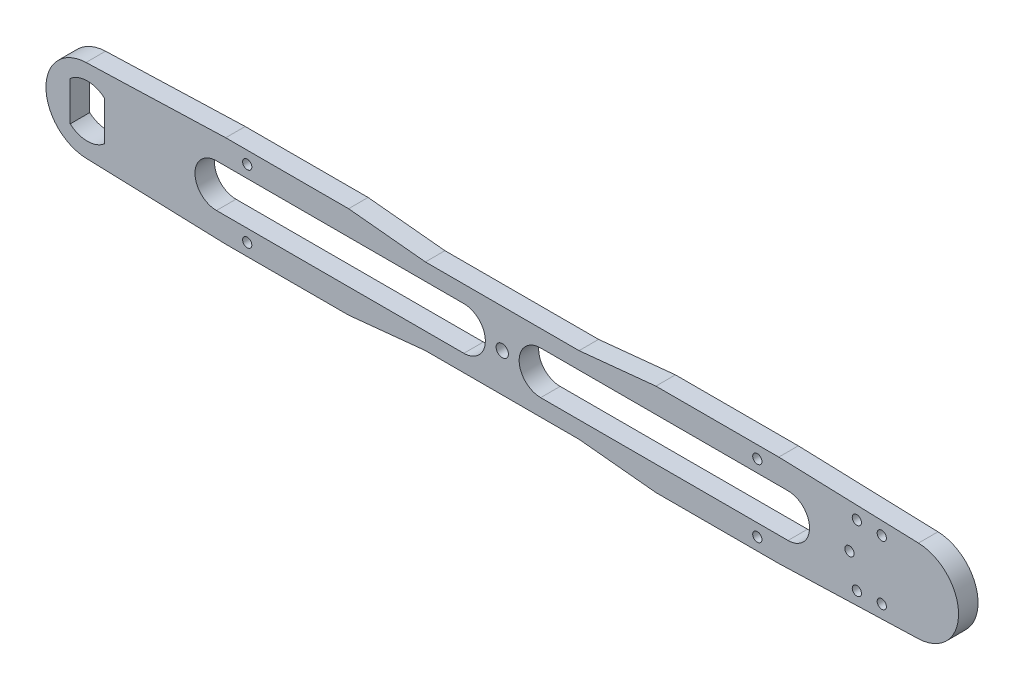
SolidWorks part; units mm, degrees
ref_plane "Alzado" through (0, 0, 0) normal (0, 0, 1) x (1, 0, 0)
ref_plane "Planta" through (0, 0, 0) normal (0, 1, 0) x (1, 0, 0)
ref_plane "Vista lateral" through (0, 0, 0) normal (1, 0, 0) x (0, 0, -1)
sketch "Croquis1" plane through (0, 0, 0) normal (0, 0, 1) x (1, 0, 0)
  line L0 (0, 0) -> (270, 0) construction
  line L1 (135, 0) -> (135, 15) construction
  line L2 (135, 15) -> (45, 15) construction
  line L3 (45, 15) -> (-0.4475, 13.4926)
  line L4 (0, 0) -> (0, 13.5) construction
  line L5 (45, 15) -> (45, 0) construction
  line L6 (45, 15) -> (85, 15)
  line L7 (85, 15) -> (110, 12.5)
  line L8 (110, 12.5) -> (160, 12.5)
  line L9 (110, -12.5) -> (160, -12.5)
  line L10 (85, -15) -> (110, -12.5)
  line L11 (45, -15) -> (85, -15)
  line L12 (45, -15) -> (-0.4475, -13.4926)
  line L13 (185, -15) -> (160, -12.5)
  line L14 (185, 15) -> (160, 12.5)
  line L15 (225, 15) -> (185, 15)
  line L16 (225, -15) -> (185, -15)
  line L17 (225, -15) -> (270.4475, -13.4926)
  line L18 (225, 15) -> (270.4475, 13.4926)
  circle A0 centre (0, 0) radius 13.5
  circle A1 centre (270, 0) radius 13.5
  point P20 (135, 12.5)
  point P21 (135, -12.5)
  dimension "D1" = 270
  dimension "D2" = 27
  dimension "D3" = 15
  dimension "D4" = 45
  dimension "D5" = 25
  dimension "D6" = 2.5
  dimension "D7" = 40
extrude "Saliente-Extruir1" add sketch "Croquis1" along normal blind 6.35 contours A0 | L17 A1 L18 L15 L14 L8 L7 L6 L3 A0 L12 L11 L10 L9 L13 L16 | A1
sketch "Croquis2" plane through (0, 0, 6.35) normal (0, 0, 1) x (1, 0, 0)
  line L0 (0, 8.5) -> (0, -8.5) construction
  line L1 (-5.6, 6.3945) -> (-5.6, -6.3945)
  line L2 (5.6, 6.3945) -> (5.6, -6.3945)
  circle A0 centre (0, 0) radius 8.5
  dimension "D1" = 17
  dimension "D2" = 5.6
extrude "Cortar-Extruir1" cut sketch "Croquis2" against normal blind 6.35 contours L0 A0 L1 | A0 L0 L2
sketch "Croquis3" plane through (0, 0, 6.35) normal (0, 0, 1) x (1, 0, 0)
  line L0 (0, 0) -> (270, 0) construction
  line L1 (135, 0) -> (135, 12.5) construction
  line L2 (110, 12.5) -> (160, 12.5) construction
  line L3 (42, 7) -> (228, 7)
  line L4 (42, -7) -> (228, -7)
  circle A0 centre (0, 0) radius 35 construction
  circle A1 centre (42, 0) radius 7
  circle A2 centre (228, 0) radius 7
  circle A3 centre (122.5, 0) radius 7
  circle A4 centre (147.5, 0) radius 7
  point P16 (135, -7)
  point P19 (135, 7)
  dimension "D1" = 70
  dimension "D2" = 14
  dimension "D3" = 12.5
extrude "Cortar-Extruir3" cut sketch "Croquis3" against normal blind 10 contours A3 L3 A1 L4 | A1 | A3 | A4 | L3 A4 L4 A2 | A2 L3
sketch "Croquis4" plane through (0, 0, 6.35) normal (0, 0, 1) x (1, 0, 0)
  line L0 (0, 0) -> (270, 0) construction
  line L1 (135, 12.5) -> (135, -12.5) construction
  line L2 (110, 12.5) -> (160, 12.5) construction
  line L3 (110, -12.5) -> (160, -12.5) construction
  line L4 (52, 15) -> (52, 0) construction
  line L5 (45, 15) -> (85, 15) construction
  circle A0 centre (52, 11) radius 1.5
  circle A1 centre (0, 0) radius 46 construction
  circle A2 centre (52, -11) radius 1.5
  circle A3 centre (218, -11) radius 1.5
  circle A4 centre (218, 11) radius 1.5
  circle A5 centre (135, 0) radius 2
  dimension "D1" = 3
  dimension "D4" = 92
  dimension "D5" = 4
  dimension "D2" = 11
  dimension "D3" = 83
extrude "Cortar-Extruir4" cut sketch "Croquis4" against normal blind 10
sketch "Croquis5" plane through (0, 0, 6.35) normal (0, 0, 1) x (1, 0, 0)
  line L0 (240, 14.5025) -> (270.4475, 13.4926) construction
  line L1 (225, 15) -> (270.4475, 13.4926) construction
  line L2 (270, 0) -> (240, 0) construction
  line L3 (240, 14.5025) -> (240, -14.5025) construction
  line L4 (240, -14.5025) -> (270.4475, -13.4926) construction
  line L5 (239.9171, 12.0038) -> (262.5427, 11.2534) construction
  line L6 (239.9171, 12.0038) -> (270.3647, 10.994) construction
  line L7 (279.5, 0) -> (283.5, 0) construction
  circle A0 centre (270, 0) radius 13.5 construction
  arc A1 (270.4475, -13.4926) -> (270.4475, 13.4926) centre (270, 0) ccw construction
  circle A2 centre (270, 0) radius 17.5 construction
  circle A3 centre (228, 0) radius 12 construction
  circle A4 centre (250.4827, 10.1526) radius 1.5 construction
  circle A5 centre (248, 0) radius 1.5
  circle A6 centre (270, 0) radius 22 construction
  circle A7 centre (250.4827, -10.1526) radius 1.5 construction
  circle A8 centre (270, 0) radius 9.5 construction
  circle A9 centre (258.7131, 9.8796) radius 1.5 construction
  circle A10 centre (258.7131, -9.8796) radius 1.5 construction
  dimension "D1" = 35
  dimension "D3" = 3
  dimension "D5" = 2.5
  dimension "D6" = 19
  dimension "D2" = 30
  dimension "D4" = 22
extrude "Cortar-Extruir5" cut sketch "Croquis5" against normal through all
sketch "Croquis6" plane through (0, 0, 6.35) normal (0, 0, 1) x (1, 0, 0)
  line L0 (270, 0) -> (248, 0) construction
  line L1 (270, 0) -> (250.3979, 9.9878) construction
  line L2 (270, 0) -> (258.5093, 9.6418) construction
  circle A0 centre (270, 0) radius 22 construction
  circle A1 centre (270, 0) radius 13.5 construction
  arc A2 (270.4475, -13.4926) -> (270.4475, 13.4926) centre (270, 0) ccw construction
  circle A3 centre (250.3979, 9.9878) radius 1.5
  circle A5 centre (258.5093, 9.6418) radius 1.5
  circle A6 centre (258.5093, -9.6418) radius 1.5
  circle A7 centre (250.3979, -9.9878) radius 1.5
  dimension "D1" = 27
  dimension "D2" = 3
  dimension "D4" = 15
  dimension "D3" = 40
extrude "Cortar-Extruir6" cut sketch "Croquis6" against normal through all
